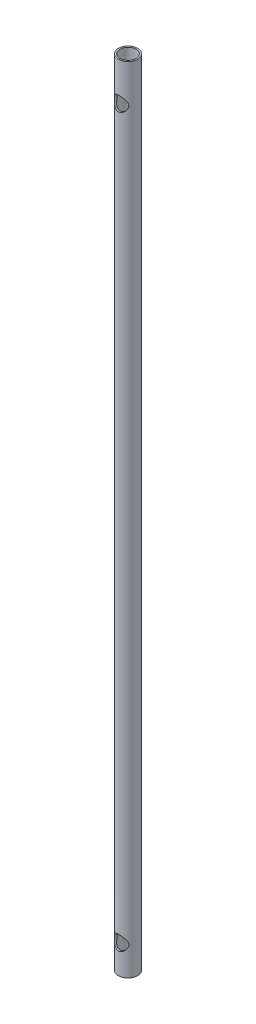
SolidWorks part; units mm, degrees
material "AISI 316 Annealed Stainless Steel Bar (SS)"
ref_plane "Front Plane" through (0, 0, 0) normal (0, 0, 1) x (1, 0, 0)
ref_plane "Top Plane" through (0, 0, 0) normal (0, 1, 0) x (1, 0, 0)
ref_plane "Right Plane" through (0, 0, 0) normal (1, 0, 0) x (0, 0, -1)
sketch "Sketch1" plane through (0, 0, 0) normal (0, 0, 1) x (1, 0, 0)
  line L0 (-5.334, 0) -> (-5.334, -527.05)
  line L1 (-5.334, -527.05) -> (-6.35, -527.05)
  line L2 (-6.35, -527.05) -> (-6.35, 0)
  line L3 (-6.35, 0) -> (-5.334, 0)
  line L4 (0, 0) -> (0, -11.7833) construction
  dimension "D1" = 5.334
  dimension "D2" = 6.35
  dimension "D3" = 527.05
revolve "Revolve1" add sketch "Sketch1" angle 360 about L4
hole_wizard "3/8 (0.375) Diameter Hole1" positions "Sketch2" profile "Sketch3" hole size "3/8" standard "ANSI Inch"
sketch "Sketch2" plane through (0, 0, 0) normal (0, 0, 1) x (1, 0, 0)
  line L0 (-6.35, -527.05) -> (6.35, -527.05) construction
  point P0 (0, -508)
  point P2 (0, -25.4)
  dimension "D1" = 25.4
  dimension "D2" = 19.05
sketch "Sketch3" plane through (0, -508, 0) normal (1, 0, 0) x (0, 1, 0)
  line L0 (0, 0) -> (0, 9.2116)
  line L1 (0, 9.2116) -> (4.7625, 6.35)
  line L2 (4.7625, 6.35) -> (4.7625, 0)
  line L5 (4.7625, 0) -> (0, 0)
  line L10 (0, 9.2116) -> (-4.7625, 6.35) construction
  line L11 (0, -6.35) -> (0, 107.95) construction
  dimension "Hole Dia." = 9.525
  dimension "Hole Depth" = 6.35
  dimension "Drill Angle" = 118
